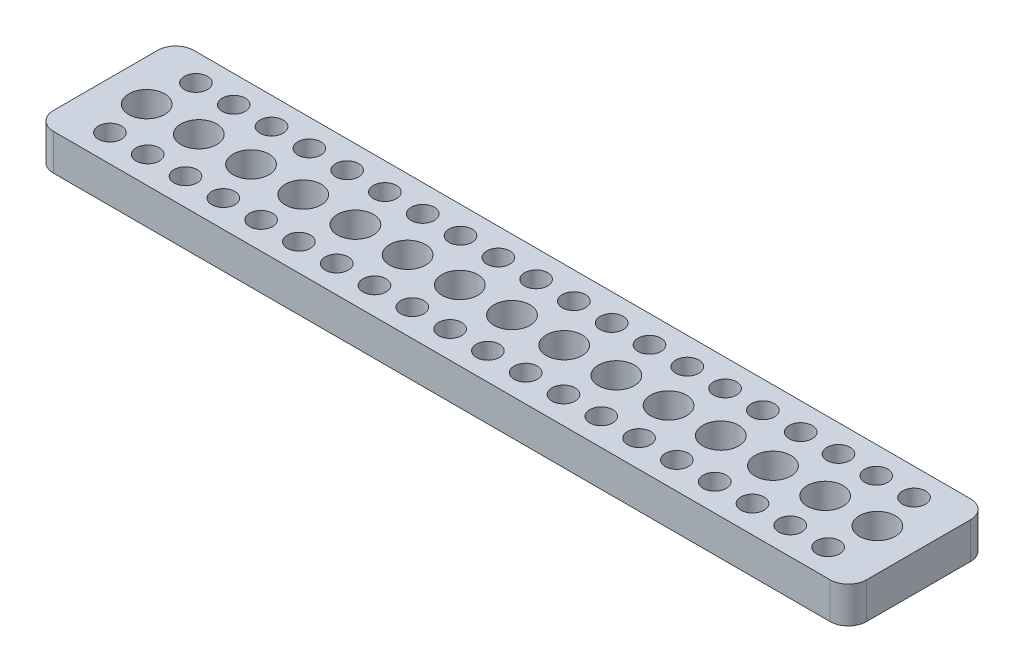
SolidWorks part; units mm, degrees
material "3.1355 (EN-AW 2024)"
ref_plane "Front" through (0, 0, 0) normal (0, 0, 1) x (1, 0, 0)
ref_plane "Top" through (0, 0, 0) normal (0, 1, 0) x (1, 0, 0)
ref_plane "Right" through (0, 0, 0) normal (1, 0, 0) x (0, 0, -1)
sketch "Эскиз1" plane through (0, 0, 0) normal (0, 1, 0) x (1, 0, 0)
  line L0 (0, 0) -> (0, 31)
  line L1 (0, 31) -> (179.605, 31)
  line L2 (179.605, 31) -> (179.605, 0)
  line L3 (179.605, 0) -> (0, 0)
  line L4 (10.475, 6) -> (18.825, 6) construction
  line L5 (18.825, 6) -> (27.175, 6) construction
  line L6 (27.175, 6) -> (35.525, 6) construction
  line L7 (35.525, 6) -> (43.875, 6) construction
  line L8 (43.875, 6) -> (52.225, 6) construction
  line L9 (52.225, 6) -> (60.575, 6) construction
  line L10 (60.575, 6) -> (68.925, 6) construction
  line L11 (68.925, 6) -> (77.275, 6) construction
  line L12 (77.275, 6) -> (85.625, 6) construction
  line L13 (85.625, 6) -> (93.975, 6) construction
  line L14 (93.975, 6) -> (102.325, 6) construction
  line L15 (102.325, 6) -> (110.675, 6) construction
  line L16 (110.675, 6) -> (119.025, 6) construction
  line L17 (119.025, 6) -> (127.375, 6) construction
  line L18 (127.375, 6) -> (135.725, 6) construction
  line L19 (135.725, 6) -> (144.075, 6) construction
  line L20 (144.075, 6) -> (152.425, 6) construction
  line L21 (152.425, 6) -> (160.775, 6) construction
  line L22 (160.775, 6) -> (169.125, 6) construction
  line L24 (9.095, 15.5) -> (20.62, 15.5) construction
  line L25 (20.625, 15.5) -> (32.15, 15.5) construction
  line L26 (32.155, 15.5) -> (43.68, 15.5) construction
  line L27 (43.685, 15.5) -> (55.21, 15.5) construction
  line L28 (55.215, 15.5) -> (66.74, 15.5) construction
  line L29 (66.745, 15.5) -> (78.27, 15.5) construction
  line L30 (78.275, 15.5) -> (89.8, 15.5) construction
  line L31 (89.805, 15.5) -> (101.33, 15.5) construction
  line L32 (101.335, 15.5) -> (112.86, 15.5) construction
  line L33 (112.865, 15.5) -> (124.39, 15.5) construction
  line L34 (124.395, 15.5) -> (135.92, 15.5) construction
  line L35 (135.925, 15.5) -> (147.45, 15.5) construction
  line L36 (147.455, 15.5) -> (158.98, 15.5) construction
  line L37 (158.985, 15.5) -> (170.51, 15.5) construction
  line L40 (160.775, 25) -> (169.125, 25) construction
  line L41 (152.425, 25) -> (160.775, 25) construction
  line L42 (144.075, 25) -> (152.425, 25) construction
  line L43 (135.725, 25) -> (144.075, 25) construction
  line L44 (127.375, 25) -> (135.725, 25) construction
  line L45 (119.025, 25) -> (127.375, 25) construction
  line L46 (110.675, 25) -> (119.025, 25) construction
  line L47 (102.325, 25) -> (110.675, 25) construction
  line L48 (93.975, 25) -> (102.325, 25) construction
  line L49 (85.625, 25) -> (93.975, 25) construction
  line L50 (77.275, 25) -> (85.625, 25) construction
  line L51 (68.925, 25) -> (77.275, 25) construction
  line L52 (60.575, 25) -> (68.925, 25) construction
  line L53 (52.225, 25) -> (60.575, 25) construction
  line L54 (43.875, 25) -> (52.225, 25) construction
  line L55 (35.525, 25) -> (43.875, 25) construction
  line L56 (27.175, 25) -> (35.525, 25) construction
  line L57 (18.825, 25) -> (27.175, 25) construction
  line L58 (10.475, 25) -> (18.825, 25) construction
  line L60 (170.515, 15.5) -> (182.04, 15.5) construction
  line L61 (169.125, 6) -> (177.475, 6) construction
  dimension "D1" = 8.35
  dimension "D3" = 10.475
  dimension "D4" = 11.525
  dimension "D5" = 9.095
  dimension "D7" = 9.5
  dimension "D8" = 6
  dimension "D9" = 31
  dimension "D10" = 6
  dimension "D11" = 179.605
  dimension "D12" = 10.48
  dimension "D2" = 20
  dimension "D6" = 15
extrude "Бобышка-Вытянуть1" add sketch "Эскиз1" along normal blind 8
hole_wizard "Отверстие обработанное метчиком 1/4-201" positions "Эскиз3" profile "Эскиз2" tap size "1/4-20" standard "Ansi Inch" end condition through all
sketch "Эскиз3" plane through (0, 0, 0) normal (0, -1, 0) x (-1, 0, 0)
  point P0 (-10.475, 25)
  point P3 (-18.825, 25)
  point P6 (-27.175, 25)
  point P9 (-35.525, 25)
  point P12 (-43.875, 25)
  point P15 (-52.225, 25)
  point P18 (-60.575, 25)
  point P21 (-68.925, 25)
  point P24 (-77.275, 25)
  point P27 (-85.625, 25)
  point P30 (-93.975, 25)
  point P33 (-102.325, 25)
  point P36 (-110.675, 25)
  point P39 (-119.025, 25)
  point P42 (-127.375, 25)
  point P45 (-135.725, 25)
  point P48 (-144.075, 25)
  point P51 (-152.425, 25)
  point P54 (-160.775, 25)
  point P57 (-169.125, 25)
  point P60 (-169.125, 6)
  point P63 (-160.775, 6)
  point P66 (-152.425, 6)
  point P69 (-144.075, 6)
  point P72 (-135.725, 6)
  point P75 (-127.375, 6)
  point P78 (-119.025, 6)
  point P81 (-110.675, 6)
  point P84 (-102.325, 6)
  point P87 (-93.975, 6)
  point P90 (-85.625, 6)
  point P93 (-77.275, 6)
  point P96 (-68.925, 6)
  point P99 (-60.575, 6)
  point P102 (-52.225, 6)
  point P105 (-43.875, 6)
  point P108 (-35.525, 6)
  point P111 (-27.175, 6)
  point P114 (-18.825, 6)
  point P117 (-10.475, 6)
sketch "Эскиз2" plane through (10.475, 0, -25) normal (1, 0, 0) x (0, 0, -1)
  line L0 (0, 0) -> (0, 8)
  line L1 (0, 8) -> (2.5527, 8)
  line L2 (2.5527, 8) -> (2.5527, 0)
  line L5 (2.5527, 0) -> (0, 0)
  line L11 (0, -6.35) -> (0, 107.95) construction
  dimension "Диаметр проходного сверла" = 5.1054
  dimension "Глубина проходного сверла" = 8
cosmetic thread "Отверстие резьбы1" parameters "D2"=6.35
cosmetic thread "Отверстие резьбы2" parameters "D2"=6.35
cosmetic thread "Отверстие резьбы3" parameters "D2"=6.35
cosmetic thread "Отверстие резьбы4" parameters "D2"=6.35
cosmetic thread "Отверстие резьбы5" parameters "D2"=6.35
cosmetic thread "Отверстие резьбы6" parameters "D2"=6.35
cosmetic thread "Отверстие резьбы7" parameters "D2"=6.35
cosmetic thread "Отверстие резьбы8" parameters "D2"=6.35
cosmetic thread "Отверстие резьбы9" parameters "D2"=6.35
cosmetic thread "Отверстие резьбы10" parameters "D2"=6.35
cosmetic thread "Отверстие резьбы11" parameters "D2"=6.35
cosmetic thread "Отверстие резьбы12" parameters "D2"=6.35
cosmetic thread "Отверстие резьбы13" parameters "D2"=6.35
cosmetic thread "Отверстие резьбы14" parameters "D2"=6.35
cosmetic thread "Отверстие резьбы15" parameters "D2"=6.35
cosmetic thread "Отверстие резьбы16" parameters "D2"=6.35
cosmetic thread "Отверстие резьбы17" parameters "D2"=6.35
cosmetic thread "Отверстие резьбы18" parameters "D2"=6.35
cosmetic thread "Отверстие резьбы19" parameters "D2"=6.35
cosmetic thread "Отверстие резьбы20" parameters "D2"=6.35
cosmetic thread "Отверстие резьбы21" parameters "D2"=6.35
cosmetic thread "Отверстие резьбы22" parameters "D2"=6.35
cosmetic thread "Отверстие резьбы23" parameters "D2"=6.35
cosmetic thread "Отверстие резьбы24" parameters "D2"=6.35
cosmetic thread "Отверстие резьбы25" parameters "D2"=6.35
cosmetic thread "Отверстие резьбы26" parameters "D2"=6.35
cosmetic thread "Отверстие резьбы27" parameters "D2"=6.35
cosmetic thread "Отверстие резьбы28" parameters "D2"=6.35
cosmetic thread "Отверстие резьбы29" parameters "D2"=6.35
cosmetic thread "Отверстие резьбы30" parameters "D2"=6.35
cosmetic thread "Отверстие резьбы31" parameters "D2"=6.35
cosmetic thread "Отверстие резьбы32" parameters "D2"=6.35
cosmetic thread "Отверстие резьбы33" parameters "D2"=6.35
cosmetic thread "Отверстие резьбы34" parameters "D2"=6.35
cosmetic thread "Отверстие резьбы35" parameters "D2"=6.35
cosmetic thread "Отверстие резьбы36" parameters "D2"=6.35
cosmetic thread "Отверстие резьбы37" parameters "D2"=6.35
cosmetic thread "Отверстие резьбы38" parameters "D2"=6.35
cosmetic thread "Отверстие резьбы39" parameters "D2"=6.35
cosmetic thread "Отверстие резьбы40" parameters "D2"=6.35
hole_wizard "Отверстие обработанное метчиком 3/8-161" positions "Эскиз5" profile "Эскиз4" tap size "3/8-16" standard "Ansi Inch" end condition through all
sketch "Эскиз5" plane through (0, 0, 0) normal (0, -1, 0) x (-1, 0, 0)
  point P0 (-9.095, 15.5)
  point P3 (-20.62, 15.5)
  point P6 (-32.15, 15.5)
  point P9 (-43.68, 15.5)
  point P12 (-55.21, 15.5)
  point P15 (-66.74, 15.5)
  point P18 (-78.27, 15.5)
  point P21 (-89.8, 15.5)
  point P24 (-101.33, 15.5)
  point P27 (-112.86, 15.5)
  point P30 (-124.39, 15.5)
  point P33 (-135.92, 15.5)
  point P36 (-147.45, 15.5)
  point P39 (-158.98, 15.5)
  point P42 (-170.51, 15.5)
sketch "Эскиз4" plane through (9.095, 0, -15.5) normal (1, 0, 0) x (0, 0, -1)
  line L0 (0, 0) -> (0, 8)
  line L1 (0, 8) -> (3.9687, 8)
  line L2 (3.9687, 8) -> (3.9687, 0)
  line L5 (3.9687, 0) -> (0, 0)
  line L11 (0, -6.35) -> (0, 107.95) construction
  dimension "Диаметр проходного сверла" = 7.9375
  dimension "Глубина проходного сверла" = 8
cosmetic thread "Отверстие резьбы41" parameters "D2"=9.525
cosmetic thread "Отверстие резьбы42" parameters "D2"=9.525
cosmetic thread "Отверстие резьбы43" parameters "D2"=9.525
cosmetic thread "Отверстие резьбы44" parameters "D2"=9.525
cosmetic thread "Отверстие резьбы45" parameters "D2"=9.525
cosmetic thread "Отверстие резьбы46" parameters "D2"=9.525
cosmetic thread "Отверстие резьбы47" parameters "D2"=9.525
cosmetic thread "Отверстие резьбы48" parameters "D2"=9.525
cosmetic thread "Отверстие резьбы49" parameters "D2"=9.525
cosmetic thread "Отверстие резьбы50" parameters "D2"=9.525
cosmetic thread "Отверстие резьбы51" parameters "D2"=9.525
cosmetic thread "Отверстие резьбы52" parameters "D2"=9.525
cosmetic thread "Отверстие резьбы53" parameters "D2"=9.525
cosmetic thread "Отверстие резьбы54" parameters "D2"=9.525
cosmetic thread "Отверстие резьбы55" parameters "D2"=9.525
fillet "Скругление1" radius 4 4 edges at (179.605, 4, -31) (179.605, 4, 0) (0, 4, -31) (0, 4, 0)
